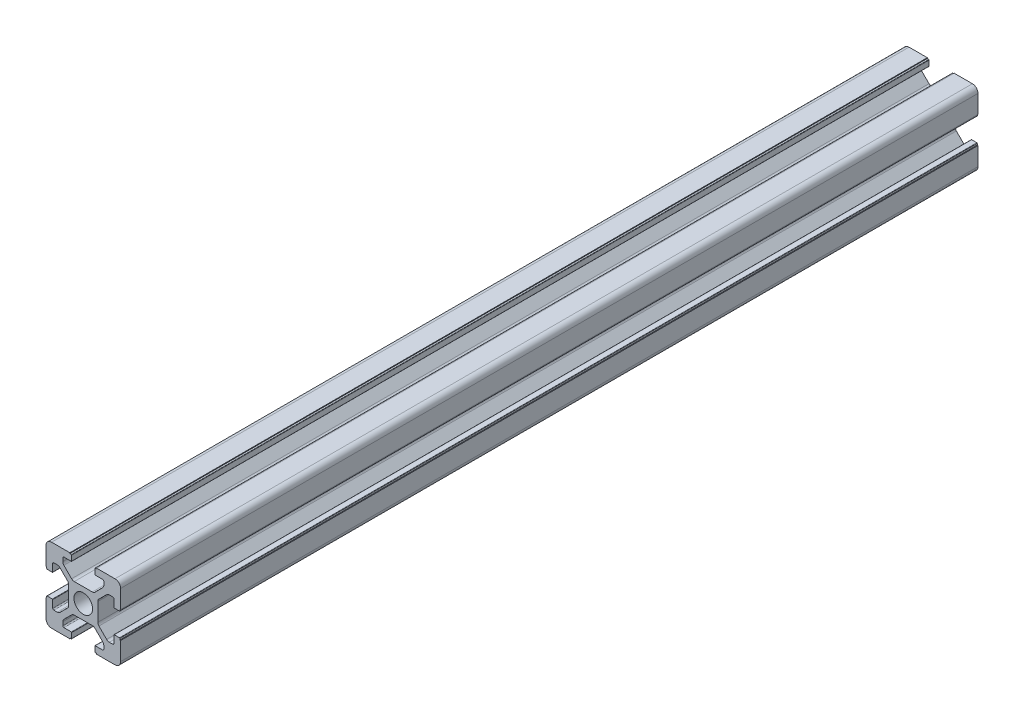
SolidWorks part; units mm, degrees
material "6063-T5"
ref_plane "前视基准面" through (0, 0, 0) normal (0, 0, 1) x (1, 0, 0)
ref_plane "上视基准面" through (0, 0, 0) normal (0, 1, 0) x (1, 0, 0)
ref_plane "右视基准面" through (0, 0, 0) normal (1, 0, 0) x (0, 0, -1)
sketch "草图1" plane through (0, 0, 0) normal (0, 0, 1) x (1, 0, 0)
  line L0 (-1.4389, 10) -> (24.3741, 10) construction
  line L1 (20, 13.6) -> (20, 20)
  line L2 (0, 0) -> (0, 6.4)
  line L3 (0, 20) -> (6.4, 20)
  line L4 (20, 0) -> (20, 6.4)
  line L5 (10, 21.5388) -> (10, -2.4017) construction
  line L6 (6.9, 18.3) -> (6.9, 19.7)
  line L7 (6.8, 18.2) -> (4.8, 18.2)
  line L8 (4.5, 17.9) -> (4.5, 16.9749)
  line L9 (4.7929, 16.2678) -> (6.8678, 14.1929)
  line L10 (7.5749, 13.9) -> (12.4251, 13.9)
  line L11 (6.8, 19.8) -> (6.4, 19.8)
  line L12 (6.4, 19.8) -> (6.4, 20)
  line L13 (0, 13.6) -> (0.2, 13.6)
  line L14 (0.2, 13.6) -> (0.2, 13.2)
  line L15 (0.3, 13.1) -> (1.7, 13.1)
  line L16 (1.8, 13.2) -> (1.8, 15.2)
  line L17 (2.1, 15.5) -> (3.0251, 15.5)
  line L18 (3.7322, 15.2071) -> (5.8071, 13.1322)
  line L19 (6.1, 12.4251) -> (6.1, 7.5749)
  line L20 (13.6, 19.8) -> (13.6, 20)
  line L21 (13.2, 19.8) -> (13.6, 19.8)
  line L22 (13.1, 18.3) -> (13.1, 19.7)
  line L23 (13.2, 18.2) -> (15.2, 18.2)
  line L24 (15.5, 17.9) -> (15.5, 16.9749)
  line L25 (15.2071, 16.2678) -> (13.1322, 14.1929)
  line L26 (0, 6.4) -> (0.2, 6.4)
  line L27 (0.2, 6.4) -> (0.2, 6.8)
  line L28 (0.3, 6.9) -> (1.7, 6.9)
  line L29 (1.8, 6.8) -> (1.8, 4.8)
  line L30 (2.1, 4.5) -> (3.0251, 4.5)
  line L31 (3.7322, 4.7929) -> (5.8071, 6.8678)
  line L32 (13.6, 20) -> (20, 20)
  line L33 (0, 13.6) -> (0, 20)
  line L34 (13.6, 0.2) -> (13.6, 0)
  line L35 (13.2, 0.2) -> (13.6, 0.2)
  line L36 (13.1, 1.7) -> (13.1, 0.3)
  line L37 (13.2, 1.8) -> (15.2, 1.8)
  line L38 (15.5, 2.1) -> (15.5, 3.0251)
  line L39 (15.2071, 3.7322) -> (13.1322, 5.8071)
  line L40 (4.5, 2.1) -> (4.5, 3.0251)
  line L41 (6.8, 1.8) -> (4.8, 1.8)
  line L42 (6.4, 0.2) -> (6.4, 0)
  line L43 (6.8, 0.2) -> (6.4, 0.2)
  line L44 (6.9, 1.7) -> (6.9, 0.3)
  line L45 (4.7929, 3.7322) -> (6.8678, 5.8071)
  line L46 (7.5749, 6.1) -> (12.4251, 6.1)
  line L47 (20, 6.4) -> (19.8, 6.4)
  line L48 (19.8, 6.4) -> (19.8, 6.8)
  line L49 (19.7, 6.9) -> (18.3, 6.9)
  line L50 (18.2, 6.8) -> (18.2, 4.8)
  line L51 (17.9, 4.5) -> (16.9749, 4.5)
  line L52 (16.2678, 4.7929) -> (14.1929, 6.8678)
  line L53 (13.9, 12.4251) -> (13.9, 7.5749)
  line L54 (16.2678, 15.2071) -> (14.1929, 13.1322)
  line L55 (17.9, 15.5) -> (16.9749, 15.5)
  line L56 (18.2, 13.2) -> (18.2, 15.2)
  line L57 (19.7, 13.1) -> (18.3, 13.1)
  line L58 (19.8, 13.6) -> (19.8, 13.2)
  line L59 (20, 13.6) -> (19.8, 13.6)
  line L60 (0, 0) -> (6.4, 0)
  line L61 (13.6, 0) -> (20, 0)
  arc A0 (6.1, 12.4251) -> (5.8071, 13.1322) centre (5.1, 12.4251) ccw
  arc A1 (7.5749, 13.9) -> (6.8678, 14.1929) centre (7.5749, 14.9) cw
  arc A2 (4.5, 16.9749) -> (4.7929, 16.2678) centre (5.5, 16.9749) ccw
  arc A3 (3.7322, 15.2071) -> (3.0251, 15.5) centre (3.0251, 14.5) ccw
  arc A4 (4.5, 17.9) -> (4.8, 18.2) centre (4.8, 17.9) cw
  arc A5 (1.8, 15.2) -> (2.1, 15.5) centre (2.1, 15.2) cw
  arc A6 (0.3, 13.1) -> (0.2, 13.2) centre (0.3, 13.2) cw
  arc A7 (6.9, 19.7) -> (6.8, 19.8) centre (6.8, 19.7) ccw
  arc A8 (1.7, 13.1) -> (1.8, 13.2) centre (1.7, 13.2) ccw
  arc A9 (6.9, 18.3) -> (6.8, 18.2) centre (6.8, 18.3) cw
  arc A10 (13.1, 19.7) -> (13.2, 19.8) centre (13.2, 19.7) cw
  arc A11 (13.1, 18.3) -> (13.2, 18.2) centre (13.2, 18.3) ccw
  arc A12 (15.5, 17.9) -> (15.2, 18.2) centre (15.2, 17.9) ccw
  arc A13 (15.5, 16.9749) -> (15.2071, 16.2678) centre (14.5, 16.9749) cw
  arc A14 (12.4251, 13.9) -> (13.1322, 14.1929) centre (12.4251, 14.9) ccw
  arc A15 (0.3, 6.9) -> (0.2, 6.8) centre (0.3, 6.8) ccw
  arc A16 (1.7, 6.9) -> (1.8, 6.8) centre (1.7, 6.8) cw
  arc A17 (1.8, 4.8) -> (2.1, 4.5) centre (2.1, 4.8) ccw
  arc A18 (3.7322, 4.7929) -> (3.0251, 4.5) centre (3.0251, 5.5) cw
  arc A19 (6.1, 7.5749) -> (5.8071, 6.8678) centre (5.1, 7.5749) cw
  arc A20 (13.1, 0.3) -> (13.2, 0.2) centre (13.2, 0.3) ccw
  arc A21 (13.1, 1.7) -> (13.2, 1.8) centre (13.2, 1.7) cw
  arc A22 (15.5, 2.1) -> (15.2, 1.8) centre (15.2, 2.1) cw
  arc A23 (15.5, 3.0251) -> (15.2071, 3.7322) centre (14.5, 3.0251) ccw
  arc A24 (12.4251, 6.1) -> (13.1322, 5.8071) centre (12.4251, 5.1) cw
  arc A25 (4.5, 2.1) -> (4.8, 1.8) centre (4.8, 2.1) ccw
  arc A26 (6.9, 0.3) -> (6.8, 0.2) centre (6.8, 0.3) cw
  arc A27 (6.9, 1.7) -> (6.8, 1.8) centre (6.8, 1.7) ccw
  arc A28 (4.5, 3.0251) -> (4.7929, 3.7322) centre (5.5, 3.0251) cw
  arc A29 (7.5749, 6.1) -> (6.8678, 5.8071) centre (7.5749, 5.1) ccw
  arc A30 (19.7, 6.9) -> (19.8, 6.8) centre (19.7, 6.8) cw
  arc A31 (18.3, 6.9) -> (18.2, 6.8) centre (18.3, 6.8) ccw
  arc A32 (18.2, 4.8) -> (17.9, 4.5) centre (17.9, 4.8) cw
  arc A33 (16.2678, 4.7929) -> (16.9749, 4.5) centre (16.9749, 5.5) ccw
  arc A34 (13.9, 7.5749) -> (14.1929, 6.8678) centre (14.9, 7.5749) ccw
  arc A35 (13.9, 12.4251) -> (14.1929, 13.1322) centre (14.9, 12.4251) cw
  arc A36 (16.2678, 15.2071) -> (16.9749, 15.5) centre (16.9749, 14.5) cw
  arc A37 (18.2, 15.2) -> (17.9, 15.5) centre (17.9, 15.2) ccw
  arc A38 (18.3, 13.1) -> (18.2, 13.2) centre (18.3, 13.2) cw
  arc A39 (19.7, 13.1) -> (19.8, 13.2) centre (19.7, 13.2) ccw
  circle A40 centre (10, 10) radius 2.5
  point P39 (0.2, 13.1)
  point P42 (6.9, 19.8)
  point P45 (1.8, 13.1)
  point P48 (6.9, 18.2)
  point P66 (10, 13.9)
  point P83 (6.1, 10)
  dimension "D19" = 1
  dimension "D20" = 1
  dimension "D21" = 0.3
  dimension "D22" = 0.1
  dimension "D23" = 5
  dimension "D1" = 20
  dimension "D2" = 20
  dimension "D3" = 10
  dimension "D4" = 10
  dimension "D5" = 1.8
  dimension "D6" = 0.5
  dimension "D7" = 1.6
  dimension "D8" = 3.1
  dimension "D9" = 6.1
  dimension "D10" = 5.5
  dimension "D11" = 3.1
  dimension "D12" = 6.1
  dimension "D13" = 5.5
  dimension "D14" = 1.8
  dimension "D15" = 0.5
  dimension "D16" = 1.5
  dimension "D17" = 45
  dimension "D18" = 1.6
extrude "凸台-拉伸1" add sketch "草图1" along normal blind 230
fillet "圆角1" radius 1.5 4 edges at (20, 0, 115) (0, 0, 115) (0, 20, 115) (20, 20, 115)
